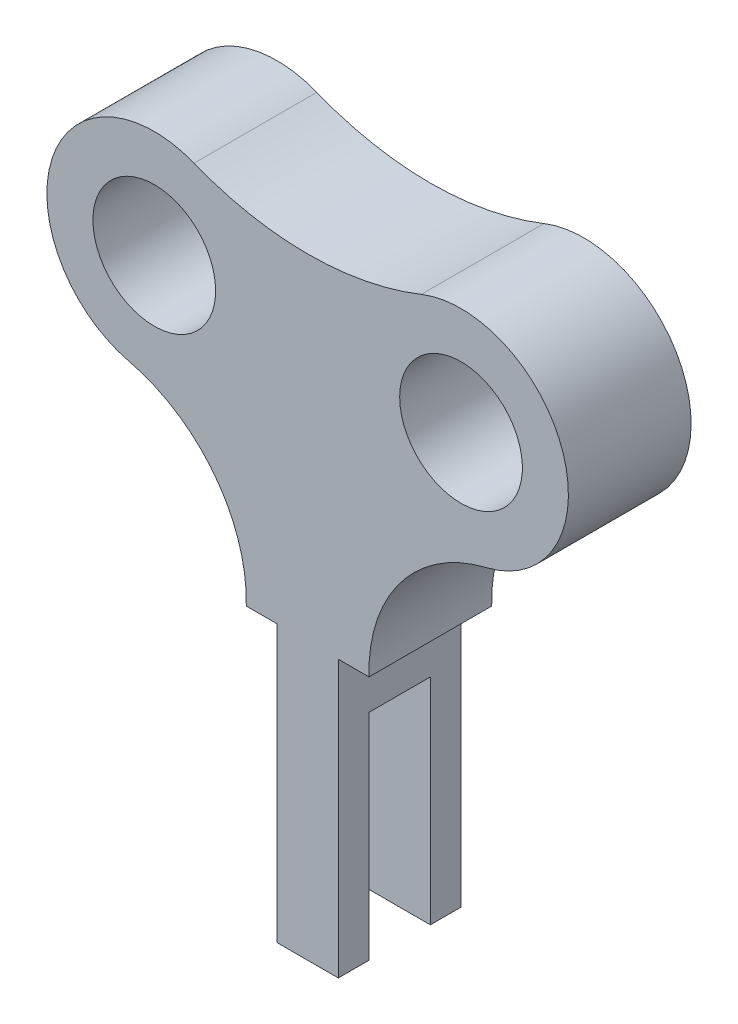
SolidWorks part; units mm, degrees
ref_plane "Front Plane" through (0, 0, 0) normal (0, 0, 1) x (1, 0, 0)
ref_plane "Top Plane" through (0, 0, 0) normal (0, 1, 0) x (1, 0, 0)
ref_plane "Right Plane" through (0, 0, 0) normal (1, 0, 0) x (0, 0, -1)
sketch "Sketch1" plane through (0, 0, 0) normal (0, 0, 1) x (1, 0, 0)
  line L0 (-30.7851, 64.5) -> (44.1631, 64.5) construction
  line L1 (-5, -22.5) -> (5, -22.5)
  line L2 (-5, -22.5) -> (-5, 22.5)
  line L4 (5, -22.5) -> (5, 22.5)
  line L5 (-5, -22.5) -> (5, 22.5) construction
  line L6 (-5, 22.5) -> (5, -22.5) construction
  line L7 (-25, 76.1552) -> (-25, -3.8264) construction
  line L8 (25, 82.184) -> (25, 46.108) construction
  line L9 (-5, 22.5) -> (-10, 22.5)
  line L10 (5, 22.5) -> (10, 22.5)
  arc A0 (-18.5185, 80.7555) -> (-29.1137, 47.4904) centre (-25, 64.5) ccw
  arc A1 (29.1137, 47.4904) -> (18.5185, 80.7555) centre (25, 64.5) ccw
  arc A7 (-18.5185, 80.7555) -> (18.5185, 80.7555) centre (0, 127.1997) ccw
  arc A8 (-10, 22.5) -> (-29.1137, 47.4904) centre (-34.9905, 23.1909) ccw
  arc A9 (29.1137, 47.4904) -> (10, 22.5) centre (34.9905, 23.1909) ccw
  point P0 (0, 0)
  point P20 (0, 0)
  point P23 (0, 0)
  dimension "D6" = 35
  dimension "D7" = 35
  dimension "D8" = 100
  dimension "D9" = 50
  dimension "D10" = 50
  dimension "D1" = 10
  dimension "D2" = 45
  dimension "D3" = 87
  dimension "D4" = 20
  dimension "D5" = 50
  dimension "D11" = 5
  dimension "D12" = 5
extrude "Boss-Extrude1" add sketch "Sketch1" along normal blind 20
sketch "Sketch3" plane through (5, 0, 0) normal (1, 0, 0) x (0, 0, -1)
  line L0 (-10, -22.5) -> (-10, 12.5) construction
  line L1 (-20, -22.5) -> (0, -22.5) construction
  line L2 (-5, -22.5) -> (-5, 12.5)
  line L3 (-15, -22.5) -> (-15, 12.5)
  line L4 (-15, 12.5) -> (-5, 12.5)
  line L5 (-5, -22.5) -> (-15, -22.5)
  dimension "D3" = 35
  dimension "D1" = 5
  dimension "D2" = 5
extrude "Cut-Extrude1" cut sketch "Sketch3" against normal through all
sketch "Sketch4" plane through (0, 0, 0) normal (0, 0, -1) x (-1, 0, 0)
  line L0 (-25, 64.5) -> (-25, -18.4271)
  line L1 (25, 64.5) -> (25, -18.4271)
  line L2 (-5, -22.5) -> (-5, 22.5) construction
  line L3 (-53.8555, 64.5) -> (52.2584, 64.5)
  arc A0 (29.1137, 47.4904) -> (18.5185, 80.7555) centre (25, 64.5) ccw construction
  circle A1 centre (-25, 64.5) radius 10
  circle A3 centre (25, 64.5) radius 10
  dimension "D4" = 20
  dimension "D5" = 20
  dimension "D1" = 50
  dimension "D2" = 20
  dimension "D3" = 20
extrude "Cut-Extrude2" cut sketch "Sketch4" against normal through all contours A1 | A3
